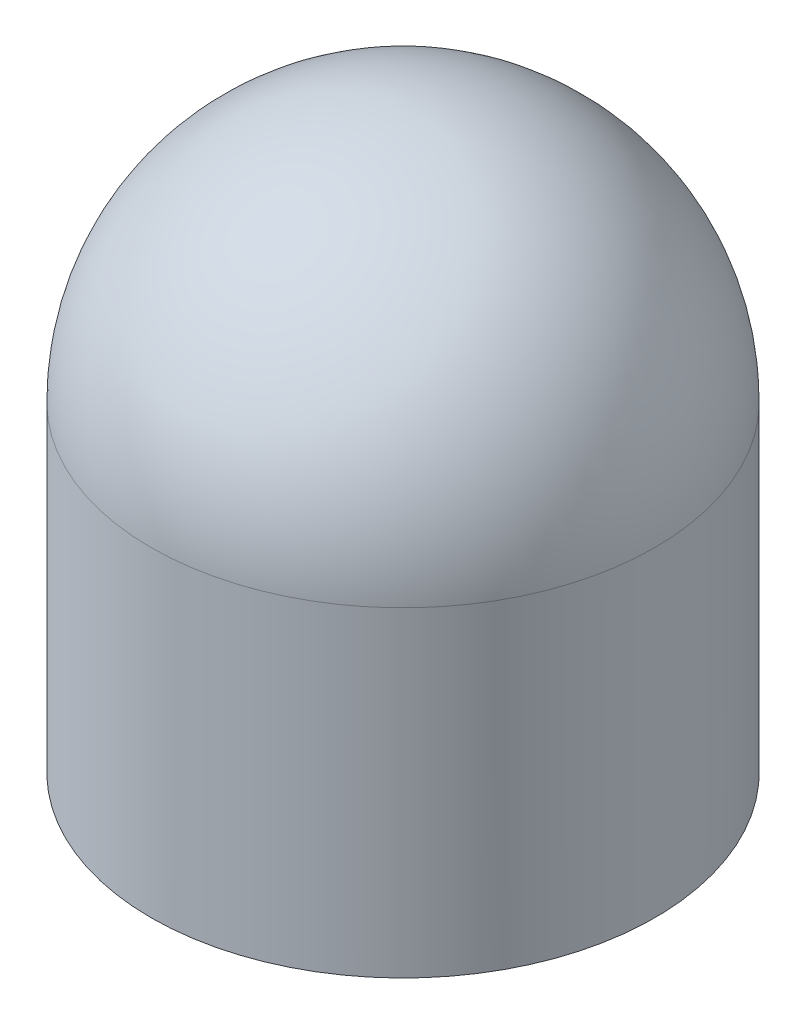
SolidWorks part; units mm, degrees
ref_plane "Front Plane" through (0, 0, 0) normal (0, 0, 1) x (1, 0, 0)
ref_plane "Top Plane" through (0, 0, 0) normal (0, 1, 0) x (1, 0, 0)
ref_plane "Right Plane" through (0, 0, 0) normal (1, 0, 0) x (0, 0, -1)
sketch "Sketch1" plane through (0, 0, 0) normal (0, 0, 1) x (1, 0, 0)
  line L0 (69.85, 0) -> (69.85, 76.2)
  line L1 (63.5, 76.2) -> (63.5, 0)
  line L2 (63.5, 0) -> (69.85, 0)
  line L3 (0, 146.05) -> (0, 139.7)
  line L5 (69.85, 0) -> (66.675, 0)
  line L6 (69.85, 0) -> (69.85, -12.7)
  line L7 (69.85, -12.7) -> (66.675, -12.7)
  line L8 (66.675, 0) -> (66.675, -12.7)
  arc A0 (63.5, 76.2) -> (0, 139.7) centre (0, 76.2) ccw
  arc A1 (69.85, 76.2) -> (0, 146.05) centre (0, 76.2) ccw
  dimension "D3" = 127
  dimension "D1" = 76.2
  dimension "D2" = 63.5
  dimension "D4" = 3.175
  dimension "D5" = 6.35
  dimension "D6" = 12.7
revolve "Revolve3" add sketch "Sketch1" angle 360 about L3
sketch "Sketch3" plane through (0, 0, 0) normal (0, -1, 0) x (-1, 0, 0)
  circle A0 centre (0, 0) radius 67.0611
  circle A1 centre (0, 0) radius 66.2673
  dimension "D1" = 0.7937
extrude "Boss-Extrude1" add sketch "Sketch3" along normal blind 12.7
fillet "Fillet2" radius 0.7937 1 edges at (0, -12.7, -66.2673)
